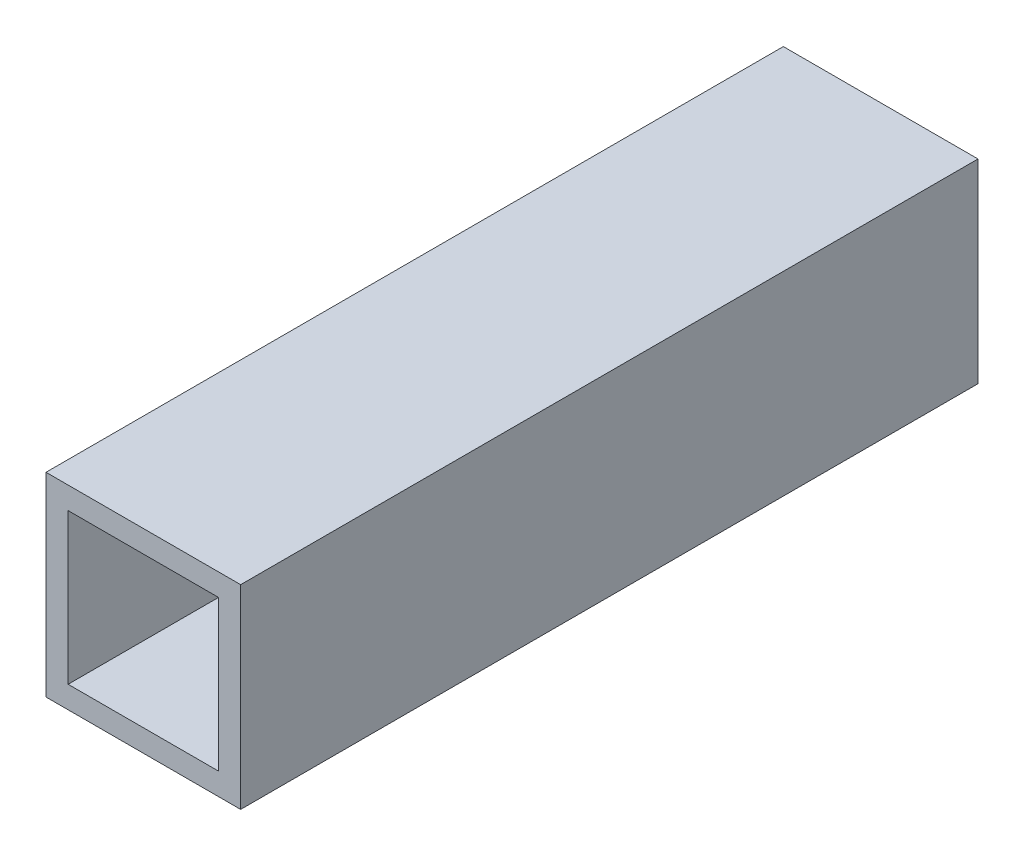
SolidWorks part; units mm, degrees
ref_plane "Front Plane" through (0, 0, 0) normal (0, 0, 1) x (1, 0, 0)
ref_plane "Top Plane" through (0, 0, 0) normal (0, 1, 0) x (1, 0, 0)
ref_plane "Right Plane" through (0, 0, 0) normal (1, 0, 0) x (0, 0, -1)
sketch "Sketch1" plane through (0, 0, 0) normal (0, 0, 1) x (1, 0, 0)
  line L0 (-2.3842, 6.3316) -> (10.8158, 6.3316)
  line L1 (-0.8842, 4.8316) -> (9.3158, 4.8316)
  line L2 (-0.8842, 4.8316) -> (-0.8842, -5.3684)
  line L3 (-0.8842, -5.3684) -> (9.3158, -5.3684)
  line L4 (9.3158, 4.8316) -> (9.3158, -5.3684)
  line L5 (10.8158, 6.3316) -> (10.8158, -6.8684)
  line L6 (-2.3842, -6.8684) -> (10.8158, -6.8684)
  line L7 (-2.3842, 6.3316) -> (-2.3842, -6.8684)
  dimension "D1" = 10.2
  dimension "D2" = 10.2
  dimension "D3" = 1.5
extrude "Boss-Extrude1" add sketch "Sketch1" along normal blind 50
